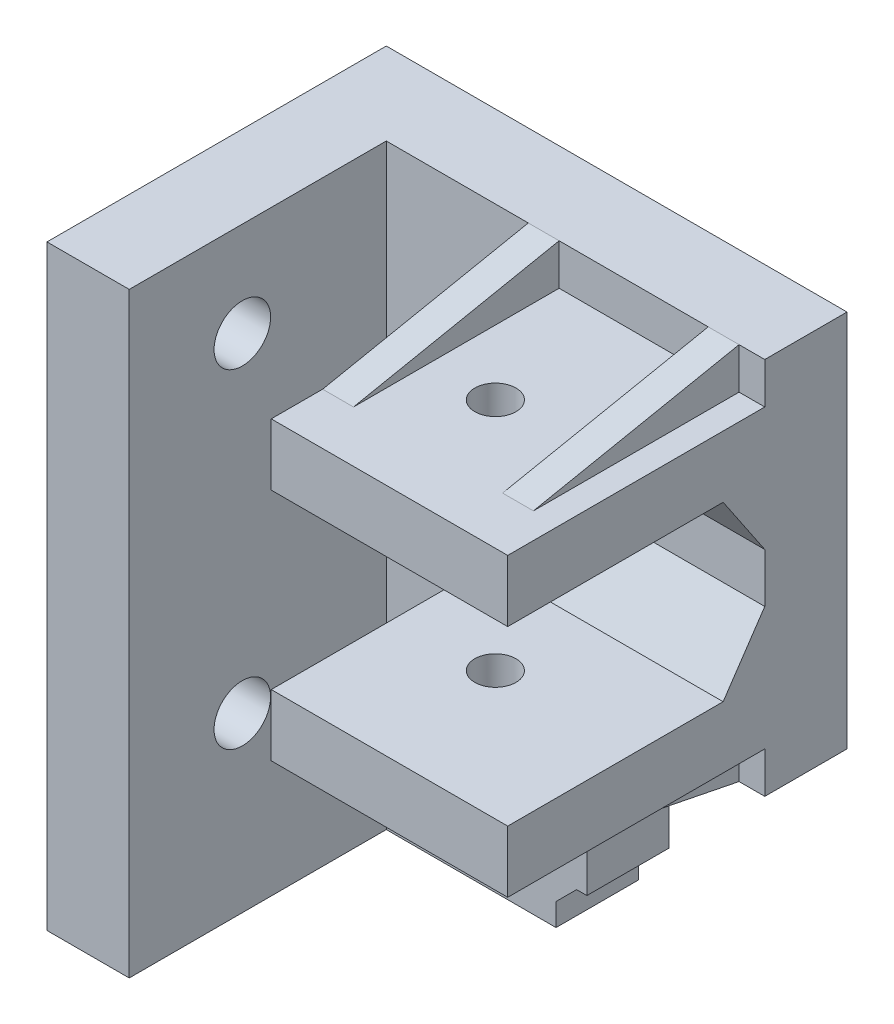
SolidWorks part; units mm, degrees
ref_plane "Plan de face" through (0, 0, 0) normal (0, 0, 1) x (1, 0, 0)
ref_plane "Plan de dessus" through (0, 0, 0) normal (0, 1, 0) x (1, 0, 0)
ref_plane "Plan de droite" through (0, 0, 0) normal (1, 0, 0) x (0, 0, -1)
sketch "Sketch1" plane through (0, 0, 0) normal (0, 0, 1) x (1, 0, 0)
  line L1 (0, 0) -> (-24.51, 0)
  line L2 (0, 0) -> (0, 148)
  line L3 (0, 148) -> (-24.51, 148)
  line L4 (-24.51, 0) -> (-24.51, 148)
  dimension "D1" = 24.51
  dimension "D2" = 148
extrude "Boss-Extrude1" add sketch "Sketch1" along normal blind 8
sketch "Sketch2" plane through (0, 0, 8) normal (0, 0, 1) x (1, 0, 0)
  line L0 (-24.51, 0) -> (0, 0) construction
  line L1 (-24.51, 148) -> (-16.51, 148)
  line L2 (-24.51, 148) -> (-24.51, 0)
  line L3 (-24.51, 0) -> (-16.51, 0)
  line L4 (-16.51, 148) -> (-16.51, 0)
  dimension "D1" = 8
extrude "Boss-Extrude2" add sketch "Sketch2" along normal blind 25
sketch "Sketch4" plane through (0, 0, 0) normal (0, 0, -1) x (-1, 0, 0)
  line L0 (0, 0) -> (0, 148) construction
  line L1 (0, 148) -> (-20.3, 148)
  line L2 (0, 148) -> (0, 111.2)
  line L3 (0, 111.2) -> (-20.3, 111.2)
  line L4 (-20.3, 148) -> (-20.3, 111.2)
  line L6 (0, 148) -> (24.51, 148) construction
  dimension "D1" = 36.8
  dimension "D2" = 20.3
extrude "Boss-Extrude3" add sketch "Sketch4" against normal up to surface (8 mm away) up to face at (-8.255, 55.5, 8)
sketch "Sketch5" plane through (0, 0, 8) normal (0, 0, 1) x (1, 0, 0)
  line L0 (20.3, 148) -> (20.3, 111.2) construction
  line L1 (20.3, 115.2) -> (-2.7, 115.2)
  line L2 (20.3, 115.2) -> (20.3, 121.2)
  line L3 (20.3, 121.2) -> (-2.7, 121.2)
  line L4 (-2.7, 115.2) -> (-2.7, 121.2)
  line L6 (20.3, 111.2) -> (0, 111.2) construction
  line L8 (20.3, 148) -> (20.3, 111.2) construction
  line L9 (20.3, 144) -> (-2.7, 144)
  line L10 (20.3, 144) -> (20.3, 138)
  line L11 (20.3, 138) -> (-2.7, 138)
  line L12 (-2.7, 144) -> (-2.7, 138)
  line L13 (20.3, 148) -> (-16.51, 148) construction
  dimension "D1" = 6
  dimension "D2" = 4
  dimension "D3" = 23
  dimension "D4" = 6
  dimension "D5" = 4
extrude "Boss-Extrude4" add sketch "Sketch5" along normal blind 25 contours L3 L4 L1 L2
sketch "Sketch6" plane through (0, 144, 0) normal (0, 1, 0) x (1, 0, 0)
  line L3 (20.3, -33) -> (20.3, -8) construction
  circle A0 centre (6.6, -20.5) radius 2
  dimension "D1" = 4
  dimension "D2" = 13.7
extrude "Cut-Extrude2" cut sketch "Sketch6" against normal up to surface (28.8 mm away) up to face at (8.8, 115.2, 20.5)
ref_plane "Plane1" through (16.3, 0, 0) normal (1, 0, 0) x (0, 0, -1)
sketch "Sketch8" plane through (16.3, 0, 0) normal (1, 0, 0) x (0, 0, -1)
  line L0 (-8, 148) -> (-28, 144)
  line L1 (-33, 144) -> (-8, 144) construction
  line L2 (-33, 0) -> (-33, 148) construction
  dimension "D1" = 5
rib "Rib1" sketch "Sketch8" sketch "Sketch8" thickness 3 extrusion direction parallel to sketch draft on no parameters "D1"=3
ref_plane "Plane2" through (0, 129.6, 0) normal (0, 1, 0) x (1, 0, 0)
mirror "Mirror1" about plane through (0, 129.6, 0) normal (0, 1, 0) of "Rib1"
ref_plane "Plane3" through (7.55, 0, 0) normal (-1, 0, 0) x (0, 0, 1)
mirror "Mirror2" about plane through (7.55, 0, 0) normal (-1, 0, 0) of "Mirror1", "Rib1"
sketch "Sketch3" plane through (0, 0, 8) normal (0, 0, 1) x (1, 0, 0)
  line L0 (0, 0) -> (0, 111.2) construction
  line L1 (0, 0) -> (0, 111.2) construction
  line L4 (-24.51, 0) -> (0, 0) construction
  circle A0 centre (-8, 8) radius 2.5
  circle A1 centre (-8, 40) radius 2.5
  circle A2 centre (-8, 100) radius 2.5
  circle A3 centre (-8, 132) radius 2.5
  dimension "D1" = 5
  dimension "D2" = 5
  dimension "D9" = 5
  dimension "D10" = 5
  dimension "D3" = 32
  dimension "D4" = 8
  dimension "D5" = 8
  dimension "D6" = 60
  dimension "D7" = 32
  dimension "D8" = 8
extrude "Cut-Extrude1" cut sketch "Sketch3" against normal blind 10
sketch "Sketch12" plane through (-24.51, 0, 0) normal (-1, 0, 0) x (0, 0, 1)
  circle A0 centre (22, 138.8) radius 2.75
  circle A1 centre (22, 106.8) radius 2.75
  circle A2 centre (22, 41.7) radius 2.75
  circle A3 centre (22, 9.7) radius 2.75
  dimension "D1" = 5.5
  dimension "D2" = 5.5
  dimension "D4" = 5.5
  dimension "D5" = 5.5
  dimension "D3" = 32
  dimension "D6" = 65.1
  dimension "D7" = 32
extrude "Cut-Extrude3" cut sketch "Sketch12" against normal up to surface (8 mm away) up to face at (-16.51, 55.5, 26.75)
sketch "Sketch13" plane through (0, 0, 0) normal (0, 0, -1) x (-1, 0, 0)
  line L1 (0, 0) -> (-5, 0)
  line L2 (0, 0) -> (0, 46)
  line L3 (0, 46) -> (-5, 46)
  line L4 (-5, 0) -> (-5, 46)
  dimension "D1" = 5
  dimension "D2" = 46
extrude "Boss-Extrude5" add sketch "Sketch13" against normal up to surface (8 mm away) up to face at (19.3625, 146, 8)
sketch "Sketch14" plane through (0, 0, 0) normal (0, 0, -1) x (-1, 0, 0)
  line L1 (0, 111.2) -> (-3, 111.2)
  line L2 (0, 111.2) -> (0, 94.2)
  line L3 (0, 94.2) -> (-3, 94.2)
  line L4 (-3, 111.2) -> (-3, 94.2)
  dimension "D1" = 3
  dimension "D2" = 17
extrude "Boss-Extrude6" add sketch "Sketch14" against normal up to surface (8 mm away) up to face at (19.3625, 146, 8)
chamfer "Chamfer1" distance 2 angle 45 3 edges at (0, 46, 4) (3, 111.2, 4) (0, 94.2, 4)
chamfer "Chamfer2" distance 6 angle 34 2 edges at (8.8, 121.2, 8) (8.8, 138, 8)
sketch "Sketch15" plane through (20.3, 0, 0) normal (1, 0, 0) x (0, 0, -1)
  line L1 (-33, 0) -> (0, 0)
  line L2 (-33, 0) -> (-33, 90)
  line L3 (-33, 90) -> (0, 90)
  line L4 (0, 0) -> (0, 90)
  dimension "D1" = 90
extrude "Cut-Extrude4" cut sketch "Sketch15" against normal blind 48
equation "\"D9@Sketch3\"=\"D1@Sketch3\""
equation "\"D10@Sketch3\"=\"D1@Sketch3\""
